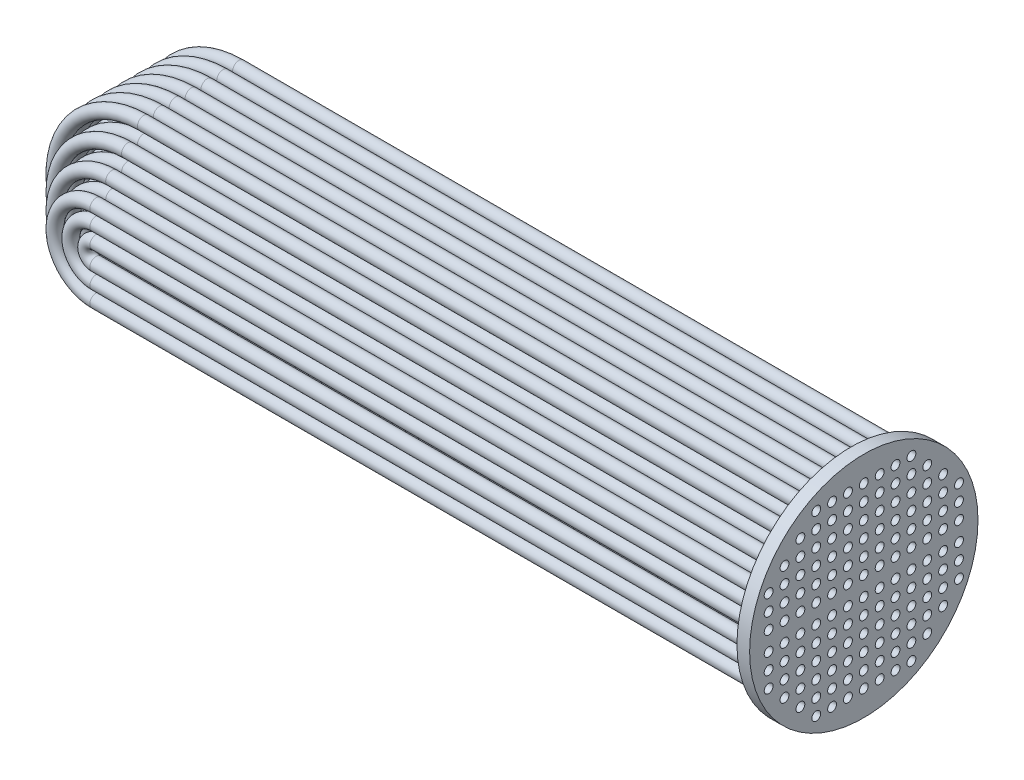
SolidWorks part; units mm, degrees
ref_plane "Front Plane" through (0, 0, 0) normal (0, 0, 1) x (1, 0, 0)
ref_plane "Top Plane" through (0, 0, 0) normal (0, 1, 0) x (1, 0, 0)
ref_plane "Right Plane" through (0, 0, 0) normal (1, 0, 0) x (0, 0, -1)
sketch "Sketch1" plane through (0, 0, 0) normal (1, 0, 0) x (0, 0, -1)
  line L0 (0, 1800) -> (0, -1973.3297) construction
  line L1 (-1800, 0) -> (1800, 0) construction
  line L2 (0, -1800) -> (0, 1973.3297) construction
  circle A0 centre (0, 0) radius 1800
  circle A1 centre (0, 150) radius 70
  circle A2 centre (250, 150) radius 70
  circle A3 centre (500, 150) radius 70
  circle A4 centre (750, 150) radius 70
  circle A5 centre (1000, 150) radius 70
  circle A6 centre (1250, 150) radius 70
  circle A7 centre (1500, 150) radius 70
  circle A8 centre (250, 400) radius 70
  circle A9 centre (500, 400) radius 70
  circle A10 centre (750, 400) radius 70
  circle A11 centre (1000, 400) radius 70
  circle A12 centre (1250, 400) radius 70
  circle A13 centre (1500, 400) radius 70
  circle A14 centre (250, 650) radius 70
  circle A15 centre (500, 650) radius 70
  circle A16 centre (750, 650) radius 70
  circle A17 centre (1000, 650) radius 70
  circle A18 centre (1250, 650) radius 70
  circle A19 centre (1500, 650) radius 70
  circle A20 centre (250, 900) radius 70
  circle A21 centre (500, 900) radius 70
  circle A22 centre (750, 900) radius 70
  circle A23 centre (1000, 900) radius 70
  circle A24 centre (1250, 900) radius 70
  circle A26 centre (250, 1150) radius 70
  circle A27 centre (500, 1150) radius 70
  circle A28 centre (750, 1150) radius 70
  circle A29 centre (1000, 1150) radius 70
  circle A32 centre (250, 1400) radius 70
  circle A33 centre (500, 1400) radius 70
  circle A34 centre (750, 1400) radius 70
  circle A38 centre (0, 400) radius 70
  circle A39 centre (0, 650) radius 70
  circle A40 centre (0, 900) radius 70
  circle A41 centre (0, 1150) radius 70
  circle A42 centre (0, 1400) radius 70
  circle A43 centre (1500, 1400) radius 70 [skipped]
  circle A44 centre (1250, 1400) radius 70 [skipped]
  circle A45 centre (1500, 1150) radius 70 [skipped]
  arc A46 (1517.7374, 967.7155) -> (1568.096, 883.7845) centre (1500, 900) ccw [skipped]
  circle A47 centre (1250, 1150) radius 70 [skipped]
  circle A48 centre (1000, 1400) radius 70 [skipped]
  circle A49 centre (-750, 1400) radius 70
  circle A50 centre (-500, 1400) radius 70
  circle A51 centre (-250, 1400) radius 70
  circle A52 centre (-1000, 1150) radius 70
  circle A53 centre (-750, 1150) radius 70
  circle A54 centre (-500, 1150) radius 70
  circle A55 centre (-250, 1150) radius 70
  circle A56 centre (-1250, 900) radius 70
  circle A57 centre (-1000, 900) radius 70
  circle A58 centre (-750, 900) radius 70
  circle A59 centre (-500, 900) radius 70
  circle A60 centre (-250, 900) radius 70
  circle A61 centre (-1500, 650) radius 70
  circle A62 centre (-1250, 650) radius 70
  circle A63 centre (-1000, 650) radius 70
  circle A64 centre (-750, 650) radius 70
  circle A65 centre (-500, 650) radius 70
  circle A66 centre (-250, 650) radius 70
  circle A67 centre (-1500, 400) radius 70
  circle A68 centre (-1250, 400) radius 70
  circle A69 centre (-1000, 400) radius 70
  circle A70 centre (-750, 400) radius 70
  circle A71 centre (-500, 400) radius 70
  circle A72 centre (-250, 400) radius 70
  circle A73 centre (-1500, 150) radius 70
  circle A74 centre (-1250, 150) radius 70
  circle A75 centre (-1000, 150) radius 70
  circle A76 centre (-750, 150) radius 70
  circle A77 centre (-500, 150) radius 70
  circle A78 centre (-250, 150) radius 70
  circle A79 centre (-250, -150) radius 70
  circle A80 centre (-500, -150) radius 70
  circle A81 centre (-750, -150) radius 70
  circle A82 centre (-1000, -150) radius 70
  circle A83 centre (-1250, -150) radius 70
  circle A84 centre (-1500, -150) radius 70
  circle A85 centre (-250, -400) radius 70
  circle A86 centre (-500, -400) radius 70
  circle A87 centre (-750, -400) radius 70
  circle A88 centre (-1000, -400) radius 70
  circle A89 centre (-1250, -400) radius 70
  circle A90 centre (-1500, -400) radius 70
  circle A91 centre (-250, -650) radius 70
  circle A92 centre (-500, -650) radius 70
  circle A93 centre (-750, -650) radius 70
  circle A94 centre (-1000, -650) radius 70
  circle A95 centre (-1250, -650) radius 70
  circle A96 centre (-1500, -650) radius 70
  circle A97 centre (-250, -900) radius 70
  circle A98 centre (-500, -900) radius 70
  circle A99 centre (-750, -900) radius 70
  circle A100 centre (-1000, -900) radius 70
  circle A101 centre (-1250, -900) radius 70
  circle A102 centre (-250, -1150) radius 70
  circle A103 centre (-500, -1150) radius 70
  circle A104 centre (-750, -1150) radius 70
  circle A105 centre (-1000, -1150) radius 70
  circle A106 centre (-250, -1400) radius 70
  circle A107 centre (-500, -1400) radius 70
  circle A108 centre (-750, -1400) radius 70
  circle A109 centre (0, -1400) radius 70
  circle A110 centre (0, -1150) radius 70
  circle A111 centre (0, -900) radius 70
  circle A112 centre (0, -650) radius 70
  circle A113 centre (0, -400) radius 70
  circle A114 centre (750, -1400) radius 70
  circle A115 centre (500, -1400) radius 70
  circle A116 centre (250, -1400) radius 70
  circle A117 centre (1000, -1150) radius 70
  circle A118 centre (750, -1150) radius 70
  circle A119 centre (500, -1150) radius 70
  circle A120 centre (250, -1150) radius 70
  circle A121 centre (1250, -900) radius 70
  circle A122 centre (1000, -900) radius 70
  circle A123 centre (750, -900) radius 70
  circle A124 centre (500, -900) radius 70
  circle A125 centre (250, -900) radius 70
  circle A126 centre (1500, -650) radius 70
  circle A127 centre (1250, -650) radius 70
  circle A128 centre (1000, -650) radius 70
  circle A129 centre (750, -650) radius 70
  circle A130 centre (500, -650) radius 70
  circle A131 centre (250, -650) radius 70
  circle A132 centre (1500, -400) radius 70
  circle A133 centre (1250, -400) radius 70
  circle A134 centre (1000, -400) radius 70
  circle A135 centre (750, -400) radius 70
  circle A136 centre (500, -400) radius 70
  circle A137 centre (250, -400) radius 70
  circle A138 centre (1500, -150) radius 70
  circle A139 centre (1250, -150) radius 70
  circle A140 centre (1000, -150) radius 70
  circle A141 centre (750, -150) radius 70
  circle A142 centre (500, -150) radius 70
  circle A143 centre (250, -150) radius 70
  circle A144 centre (0, -150) radius 70
  point P6 (0, 150)
  point P8 (0, 400)
  point P9 (0, 650)
  point P10 (0, 900)
  point P11 (0, 1130.5078)
  point P291 (0, -1130.5078)
  point P292 (0, -900)
  point P293 (0, -650)
  point P294 (0, -400)
  point P295 (0, -150)
  dimension "D1" = 3600
  dimension "D2" = 140
  dimension "D3" = 7
  dimension "D4" = 6
extrude "Boss-Extrude15" add sketch "Sketch1" along normal blind 200
sketch "Sketch3" plane through (0, 0, 0) normal (-1, 0, 0) x (0, 0, 1)
  line L0 (1800, 0) -> (-1800, 0) construction
  line L1 (0, 1800) -> (0, -1800) construction
  circle A0 centre (0, 150) radius 100
  circle A1 centre (250, 150) radius 100
  circle A2 centre (500, 150) radius 100
  circle A3 centre (750, 150) radius 100
  circle A4 centre (1000, 150) radius 100
  circle A5 centre (1250, 150) radius 100
  circle A6 centre (1500, 150) radius 100
  circle A7 centre (250, 400) radius 100
  circle A8 centre (500, 400) radius 100
  circle A9 centre (750, 400) radius 100
  circle A10 centre (1000, 400) radius 100
  circle A11 centre (1250, 400) radius 100
  circle A12 centre (1500, 400) radius 100
  circle A13 centre (250, 650) radius 100
  circle A14 centre (500, 650) radius 100
  circle A15 centre (750, 650) radius 100
  circle A16 centre (1000, 650) radius 100
  circle A17 centre (1250, 650) radius 100
  circle A18 centre (1500, 650) radius 100
  circle A19 centre (250, 900) radius 100
  circle A20 centre (500, 900) radius 100
  circle A21 centre (750, 900) radius 100
  circle A22 centre (1000, 900) radius 100
  circle A23 centre (1250, 900) radius 100
  circle A25 centre (250, 1150) radius 100
  circle A26 centre (500, 1150) radius 100
  circle A27 centre (750, 1150) radius 100
  circle A28 centre (1000, 1150) radius 100
  circle A31 centre (250, 1400) radius 100
  circle A32 centre (500, 1400) radius 100
  circle A33 centre (750, 1400) radius 100
  circle A37 centre (0, 400) radius 100
  circle A38 centre (0, 650) radius 100
  circle A39 centre (0, 900) radius 100
  circle A40 centre (0, 1150) radius 100
  circle A41 centre (0, 1400) radius 100
  circle A42 centre (1500, 1400) radius 100 [skipped]
  circle A43 centre (1500, 1150) radius 100 [skipped]
  circle A44 centre (1250, 1400) radius 100 [skipped]
  circle A45 centre (1500, 900) radius 100 [skipped]
  circle A46 centre (1250, 1150) radius 100 [skipped]
  circle A47 centre (1000, 1400) radius 100 [skipped]
  circle A48 centre (0, 150) radius 70
  circle A49 centre (250, 150) radius 70
  circle A50 centre (500, 150) radius 70
  circle A51 centre (750, 150) radius 70
  circle A52 centre (1000, 150) radius 70
  circle A53 centre (1250, 150) radius 70
  circle A54 centre (1500, 150) radius 70
  circle A55 centre (250, 400) radius 70
  circle A56 centre (500, 400) radius 70
  circle A57 centre (750, 400) radius 70
  circle A58 centre (1000, 400) radius 70
  circle A59 centre (1250, 400) radius 70
  circle A60 centre (1500, 400) radius 70
  circle A61 centre (250, 650) radius 70
  circle A62 centre (500, 650) radius 70
  circle A63 centre (750, 650) radius 70
  circle A64 centre (1000, 650) radius 70
  circle A65 centre (1250, 650) radius 70
  circle A66 centre (1500, 650) radius 70
  circle A67 centre (250, 900) radius 70
  circle A68 centre (500, 900) radius 70
  circle A69 centre (750, 900) radius 70
  circle A70 centre (1000, 900) radius 70
  circle A71 centre (1250, 900) radius 70
  circle A73 centre (250, 1150) radius 70
  circle A74 centre (500, 1150) radius 70
  circle A75 centre (750, 1150) radius 70
  circle A76 centre (1000, 1150) radius 70
  circle A79 centre (250, 1400) radius 70
  circle A80 centre (500, 1400) radius 70
  circle A81 centre (750, 1400) radius 70
  circle A85 centre (0, 400) radius 70
  circle A86 centre (0, 650) radius 70
  circle A87 centre (0, 900) radius 70
  circle A88 centre (0, 1150) radius 70
  circle A89 centre (0, 1400) radius 70
  circle A90 centre (1500, 900) radius 70 [skipped]
  circle A91 centre (1250, 1150) radius 70 [skipped]
  circle A92 centre (1000, 1400) radius 70 [skipped]
  circle A93 centre (1250, 1400) radius 70 [skipped]
  circle A94 centre (1500, 1150) radius 70 [skipped]
  circle A95 centre (1500, 1400) radius 70 [skipped]
  circle A97 centre (-750, 1400) radius 70
  circle A98 centre (-500, 1400) radius 70
  circle A99 centre (-250, 1400) radius 70
  circle A100 centre (-1000, 1150) radius 70
  circle A101 centre (-750, 1150) radius 70
  circle A102 centre (-500, 1150) radius 70
  circle A103 centre (-250, 1150) radius 70
  circle A104 centre (-1250, 900) radius 70
  circle A105 centre (-1000, 900) radius 70
  circle A106 centre (-750, 900) radius 70
  circle A107 centre (-500, 900) radius 70
  circle A108 centre (-250, 900) radius 70
  circle A109 centre (-1500, 650) radius 70
  circle A110 centre (-1250, 650) radius 70
  circle A111 centre (-1000, 650) radius 70
  circle A112 centre (-750, 650) radius 70
  circle A113 centre (-500, 650) radius 70
  circle A114 centre (-250, 650) radius 70
  circle A115 centre (-1500, 400) radius 70
  circle A116 centre (-1250, 400) radius 70
  circle A117 centre (-1000, 400) radius 70
  circle A118 centre (-750, 400) radius 70
  circle A119 centre (-500, 400) radius 70
  circle A120 centre (-250, 400) radius 70
  circle A121 centre (-1500, 150) radius 70
  circle A122 centre (-1250, 150) radius 70
  circle A123 centre (-1000, 150) radius 70
  circle A124 centre (-750, 150) radius 70
  circle A125 centre (-500, 150) radius 70
  circle A126 centre (-250, 150) radius 70
  circle A127 centre (-750, 1400) radius 100
  circle A128 centre (-500, 1400) radius 100
  circle A129 centre (-250, 1400) radius 100
  circle A130 centre (-1000, 1150) radius 100
  circle A131 centre (-750, 1150) radius 100
  circle A132 centre (-500, 1150) radius 100
  circle A133 centre (-250, 1150) radius 100
  circle A134 centre (-1250, 900) radius 100
  circle A135 centre (-1000, 900) radius 100
  circle A136 centre (-750, 900) radius 100
  circle A137 centre (-500, 900) radius 100
  circle A138 centre (-250, 900) radius 100
  circle A139 centre (-1500, 650) radius 100
  circle A140 centre (-1250, 650) radius 100
  circle A141 centre (-1000, 650) radius 100
  circle A142 centre (-750, 650) radius 100
  circle A143 centre (-500, 650) radius 100
  circle A144 centre (-250, 650) radius 100
  circle A145 centre (-1500, 400) radius 100
  circle A146 centre (-1250, 400) radius 100
  circle A147 centre (-1000, 400) radius 100
  circle A148 centre (-750, 400) radius 100
  circle A149 centre (-500, 400) radius 100
  circle A150 centre (-250, 400) radius 100
  circle A151 centre (-1500, 150) radius 100
  circle A152 centre (-1250, 150) radius 100
  circle A153 centre (-1000, 150) radius 100
  circle A154 centre (-750, 150) radius 100
  circle A155 centre (-500, 150) radius 100
  circle A156 centre (-250, 150) radius 100
  circle A157 centre (-250, -150) radius 100
  circle A158 centre (-500, -150) radius 100
  circle A159 centre (-750, -150) radius 100
  circle A160 centre (-1000, -150) radius 100
  circle A161 centre (-1250, -150) radius 100
  circle A162 centre (-1500, -150) radius 100
  circle A163 centre (-250, -400) radius 100
  circle A164 centre (-500, -400) radius 100
  circle A165 centre (-750, -400) radius 100
  circle A166 centre (-1000, -400) radius 100
  circle A167 centre (-1250, -400) radius 100
  circle A168 centre (-1500, -400) radius 100
  circle A169 centre (-250, -650) radius 100
  circle A170 centre (-500, -650) radius 100
  circle A171 centre (-750, -650) radius 100
  circle A172 centre (-1000, -650) radius 100
  circle A173 centre (-1250, -650) radius 100
  circle A174 centre (-1500, -650) radius 100
  circle A175 centre (-250, -900) radius 100
  circle A176 centre (-500, -900) radius 100
  circle A177 centre (-750, -900) radius 100
  circle A178 centre (-1000, -900) radius 100
  circle A179 centre (-1250, -900) radius 100
  circle A180 centre (-250, -1150) radius 100
  circle A181 centre (-500, -1150) radius 100
  circle A182 centre (-750, -1150) radius 100
  circle A183 centre (-1000, -1150) radius 100
  circle A184 centre (-250, -1400) radius 100
  circle A185 centre (-500, -1400) radius 100
  circle A186 centre (-750, -1400) radius 100
  circle A187 centre (-250, -150) radius 70
  circle A188 centre (-500, -150) radius 70
  circle A189 centre (-750, -150) radius 70
  circle A190 centre (-1000, -150) radius 70
  circle A191 centre (-1250, -150) radius 70
  circle A192 centre (-1500, -150) radius 70
  circle A193 centre (-250, -400) radius 70
  circle A194 centre (-500, -400) radius 70
  circle A195 centre (-750, -400) radius 70
  circle A196 centre (-1000, -400) radius 70
  circle A197 centre (-1250, -400) radius 70
  circle A198 centre (-1500, -400) radius 70
  circle A199 centre (-250, -650) radius 70
  circle A200 centre (-500, -650) radius 70
  circle A201 centre (-750, -650) radius 70
  circle A202 centre (-1000, -650) radius 70
  circle A203 centre (-1250, -650) radius 70
  circle A204 centre (-1500, -650) radius 70
  circle A205 centre (-250, -900) radius 70
  circle A206 centre (-500, -900) radius 70
  circle A207 centre (-750, -900) radius 70
  circle A208 centre (-1000, -900) radius 70
  circle A209 centre (-1250, -900) radius 70
  circle A210 centre (-250, -1150) radius 70
  circle A211 centre (-500, -1150) radius 70
  circle A212 centre (-750, -1150) radius 70
  circle A213 centre (-1000, -1150) radius 70
  circle A214 centre (-250, -1400) radius 70
  circle A215 centre (-500, -1400) radius 70
  circle A216 centre (-750, -1400) radius 70
  circle A217 centre (0, -1400) radius 70
  circle A218 centre (0, -1150) radius 70
  circle A219 centre (0, -900) radius 70
  circle A220 centre (0, -650) radius 70
  circle A221 centre (0, -400) radius 70
  circle A222 centre (750, -1400) radius 70
  circle A223 centre (500, -1400) radius 70
  circle A224 centre (250, -1400) radius 70
  circle A225 centre (1000, -1150) radius 70
  circle A226 centre (750, -1150) radius 70
  circle A227 centre (500, -1150) radius 70
  circle A228 centre (250, -1150) radius 70
  circle A229 centre (1250, -900) radius 70
  circle A230 centre (1000, -900) radius 70
  circle A231 centre (750, -900) radius 70
  circle A232 centre (500, -900) radius 70
  circle A233 centre (250, -900) radius 70
  circle A234 centre (1500, -650) radius 70
  circle A235 centre (1250, -650) radius 70
  circle A236 centre (1000, -650) radius 70
  circle A237 centre (750, -650) radius 70
  circle A238 centre (500, -650) radius 70
  circle A239 centre (250, -650) radius 70
  circle A240 centre (1500, -400) radius 70
  circle A241 centre (1250, -400) radius 70
  circle A242 centre (1000, -400) radius 70
  circle A243 centre (750, -400) radius 70
  circle A244 centre (500, -400) radius 70
  circle A245 centre (250, -400) radius 70
  circle A246 centre (1500, -150) radius 70
  circle A247 centre (1250, -150) radius 70
  circle A248 centre (1000, -150) radius 70
  circle A249 centre (750, -150) radius 70
  circle A250 centre (500, -150) radius 70
  circle A251 centre (250, -150) radius 70
  circle A252 centre (0, -150) radius 70
  circle A253 centre (0, -1400) radius 100
  circle A254 centre (0, -1150) radius 100
  circle A255 centre (0, -900) radius 100
  circle A256 centre (0, -650) radius 100
  circle A257 centre (0, -400) radius 100
  circle A258 centre (750, -1400) radius 100
  circle A259 centre (500, -1400) radius 100
  circle A260 centre (250, -1400) radius 100
  circle A261 centre (1000, -1150) radius 100
  circle A262 centre (750, -1150) radius 100
  circle A263 centre (500, -1150) radius 100
  circle A264 centre (250, -1150) radius 100
  circle A265 centre (1250, -900) radius 100
  circle A266 centre (1000, -900) radius 100
  circle A267 centre (750, -900) radius 100
  circle A268 centre (500, -900) radius 100
  circle A269 centre (250, -900) radius 100
  circle A270 centre (1500, -650) radius 100
  circle A271 centre (1250, -650) radius 100
  circle A272 centre (1000, -650) radius 100
  circle A273 centre (750, -650) radius 100
  circle A274 centre (500, -650) radius 100
  circle A275 centre (250, -650) radius 100
  circle A276 centre (1500, -400) radius 100
  circle A277 centre (1250, -400) radius 100
  circle A278 centre (1000, -400) radius 100
  circle A279 centre (750, -400) radius 100
  circle A280 centre (500, -400) radius 100
  circle A281 centre (250, -400) radius 100
  circle A282 centre (1500, -150) radius 100
  circle A283 centre (1250, -150) radius 100
  circle A284 centre (1000, -150) radius 100
  circle A285 centre (750, -150) radius 100
  circle A286 centre (500, -150) radius 100
  circle A287 centre (250, -150) radius 100
  circle A288 centre (0, -150) radius 100
  dimension "D1" = 7
  dimension "D3" = 7
  dimension "D2" = 6
  dimension "D4" = 6
extrude "Boss-Extrude16" add sketch "Sketch3" along normal blind 10400
ref_plane "Plane1" through (-10400, 0, 0) normal (-1, 0, 0) x (0, 0, 1)
sketch "Sketch4" plane through (-10400, 0, 0) normal (-1, 0, 0) x (0, 0, 1)
  line L0 (0, 1800) -> (0, -1800) construction
  line L1 (0, -1800) -> (-1800, 0) construction
  line L2 (-1800, 0) -> (1800, 0) construction
  line L3 (0, -1800) -> (1800, 0) construction
  circle A0 centre (0, 150) radius 70
  circle A1 centre (0, 150) radius 100
  circle A2 centre (250, 150) radius 100
  circle A3 centre (250, 150) radius 70
  circle A4 centre (500, 150) radius 100
  circle A5 centre (500, 150) radius 70
  circle A6 centre (750, 150) radius 100
  circle A7 centre (750, 150) radius 70
  circle A8 centre (1000, 150) radius 100
  circle A9 centre (1000, 150) radius 70
  circle A10 centre (1250, 150) radius 100
  circle A11 centre (1250, 150) radius 70
  circle A12 centre (1500, 150) radius 100
  circle A13 centre (1500, 150) radius 70
  circle A14 centre (250, 400) radius 100
  circle A15 centre (250, 400) radius 70
  circle A16 centre (500, 400) radius 100
  circle A17 centre (500, 400) radius 70
  circle A18 centre (750, 400) radius 100
  circle A19 centre (750, 400) radius 70
  circle A20 centre (1000, 400) radius 100
  circle A21 centre (1000, 400) radius 70
  circle A22 centre (1250, 400) radius 100
  circle A23 centre (1250, 400) radius 70
  circle A24 centre (1500, 400) radius 100
  circle A25 centre (1500, 400) radius 70
  circle A26 centre (250, 650) radius 100
  circle A27 centre (250, 650) radius 70
  circle A28 centre (500, 650) radius 100
  circle A29 centre (500, 650) radius 70
  circle A30 centre (750, 650) radius 100
  circle A31 centre (750, 650) radius 70
  circle A32 centre (1000, 650) radius 100
  circle A33 centre (1000, 650) radius 70
  circle A34 centre (1250, 650) radius 100
  circle A35 centre (1250, 650) radius 70
  circle A36 centre (1500, 650) radius 100
  circle A37 centre (1500, 650) radius 70
  circle A38 centre (250, 900) radius 100
  circle A39 centre (250, 900) radius 70
  circle A40 centre (500, 900) radius 100
  circle A41 centre (500, 900) radius 70
  circle A42 centre (750, 900) radius 100
  circle A43 centre (750, 900) radius 70
  circle A44 centre (1000, 900) radius 100
  circle A45 centre (1000, 900) radius 70
  circle A46 centre (1250, 900) radius 100
  circle A47 centre (1250, 900) radius 70
  circle A50 centre (250, 1150) radius 100
  circle A51 centre (250, 1150) radius 70
  circle A52 centre (500, 1150) radius 100
  circle A53 centre (500, 1150) radius 70
  circle A54 centre (750, 1150) radius 100
  circle A55 centre (750, 1150) radius 70
  circle A56 centre (1000, 1150) radius 100
  circle A57 centre (1000, 1150) radius 70
  circle A62 centre (250, 1400) radius 100
  circle A63 centre (250, 1400) radius 70
  circle A64 centre (500, 1400) radius 100
  circle A65 centre (500, 1400) radius 70
  circle A66 centre (750, 1400) radius 100
  circle A67 centre (750, 1400) radius 70
  circle A74 centre (0, 400) radius 100
  circle A75 centre (0, 400) radius 70
  circle A76 centre (0, 650) radius 100
  circle A77 centre (0, 650) radius 70
  circle A78 centre (0, 900) radius 100
  circle A79 centre (0, 900) radius 70
  circle A80 centre (0, 1150) radius 100
  circle A81 centre (0, 1150) radius 70
  circle A82 centre (0, 1400) radius 100
  circle A83 centre (0, 1400) radius 70
  circle A84 centre (1500, 900) radius 100 [skipped]
  circle A85 centre (1500, 900) radius 70 [skipped]
  circle A86 centre (1250, 1150) radius 100 [skipped]
  circle A87 centre (1250, 1150) radius 70 [skipped]
  circle A88 centre (1000, 1400) radius 100 [skipped]
  circle A89 centre (1000, 1400) radius 70 [skipped]
  circle A90 centre (1250, 1400) radius 100 [skipped]
  circle A91 centre (1250, 1400) radius 70 [skipped]
  circle A92 centre (1500, 1400) radius 100 [skipped]
  circle A93 centre (1500, 1400) radius 70 [skipped]
  circle A94 centre (1500, 1150) radius 100 [skipped]
  circle A95 centre (1500, 1150) radius 70 [skipped]
  circle A97 centre (-750, 1400) radius 70
  circle A98 centre (-750, 1400) radius 100
  circle A99 centre (-500, 1400) radius 70
  circle A100 centre (-500, 1400) radius 100
  circle A101 centre (-250, 1400) radius 70
  circle A102 centre (-250, 1400) radius 100
  circle A103 centre (-1000, 1150) radius 70
  circle A104 centre (-1000, 1150) radius 100
  circle A105 centre (-750, 1150) radius 70
  circle A106 centre (-750, 1150) radius 100
  circle A107 centre (-500, 1150) radius 70
  circle A108 centre (-500, 1150) radius 100
  circle A109 centre (-250, 1150) radius 70
  circle A110 centre (-250, 1150) radius 100
  circle A111 centre (-1250, 900) radius 70
  circle A112 centre (-1250, 900) radius 100
  circle A113 centre (-1000, 900) radius 70
  circle A114 centre (-1000, 900) radius 100
  circle A115 centre (-750, 900) radius 70
  circle A116 centre (-750, 900) radius 100
  circle A117 centre (-500, 900) radius 70
  circle A118 centre (-500, 900) radius 100
  circle A119 centre (-250, 900) radius 70
  circle A120 centre (-250, 900) radius 100
  circle A121 centre (-1500, 650) radius 70
  circle A122 centre (-1500, 650) radius 100
  circle A123 centre (-1250, 650) radius 70
  circle A124 centre (-1250, 650) radius 100
  circle A125 centre (-1000, 650) radius 70
  circle A126 centre (-1000, 650) radius 100
  circle A127 centre (-750, 650) radius 70
  circle A128 centre (-750, 650) radius 100
  circle A129 centre (-500, 650) radius 70
  circle A130 centre (-500, 650) radius 100
  circle A131 centre (-250, 650) radius 70
  circle A132 centre (-250, 650) radius 100
  circle A133 centre (-1500, 400) radius 70
  circle A134 centre (-1500, 400) radius 100
  circle A135 centre (-1250, 400) radius 70
  circle A136 centre (-1250, 400) radius 100
  circle A137 centre (-1000, 400) radius 70
  circle A138 centre (-1000, 400) radius 100
  circle A139 centre (-750, 400) radius 70
  circle A140 centre (-750, 400) radius 100
  circle A141 centre (-500, 400) radius 70
  circle A142 centre (-500, 400) radius 100
  circle A143 centre (-250, 400) radius 70
  circle A144 centre (-250, 400) radius 100
  circle A145 centre (-1500, 150) radius 70
  circle A146 centre (-1500, 150) radius 100
  circle A147 centre (-1250, 150) radius 70
  circle A148 centre (-1250, 150) radius 100
  circle A149 centre (-1000, 150) radius 70
  circle A150 centre (-1000, 150) radius 100
  circle A151 centre (-750, 150) radius 70
  circle A152 centre (-750, 150) radius 100
  circle A153 centre (-500, 150) radius 70
  circle A154 centre (-500, 150) radius 100
  circle A155 centre (-250, 150) radius 70
  circle A156 centre (-250, 150) radius 100
  dimension "D1" = 7
  dimension "D2" = 6
revolve "Revolve1" add sketch "Sketch4" angle 180 about L2
sketch "Sketch5" plane through (0, 0, 0) normal (-1, 0, 0) x (0, 0, 1)
  line L0 (800, 58.9097) -> (1000, 58.9097)
  line L5 (-1000, 58.9097) -> (-800, 58.9097)
  line L6 (-1000, 58.9097) -> (-1000, -58.9097)
  line L17 (-1000, -58.9097) -> (-800, -58.9097)
  line L18 (1000, 58.9097) -> (1000, -58.9097)
  line L19 (-1000, 58.9097) -> (-800, 47.1277) construction
  line L20 (-1000, -58.9097) -> (-800, -47.1277) construction
  line L22 (-800, 58.9097) -> (-800, -58.9097)
  line L24 (800, 58.9097) -> (800, -58.9097)
  line L27 (800, 47.1277) -> (1000, 58.9097) construction
  line L28 (800, -47.1277) -> (1000, -58.9097) construction
  line L29 (800, -58.9097) -> (1000, -58.9097)
  point P0 (0, 0)
  point P1 (0, 0)
  point P6 (0, 0)
  point P8 (0, 0)
  dimension "D1" = 2000
  dimension "D2" = 1600
extrude "Boss-Extrude17" add sketch "Sketch5" along normal blind 10400
